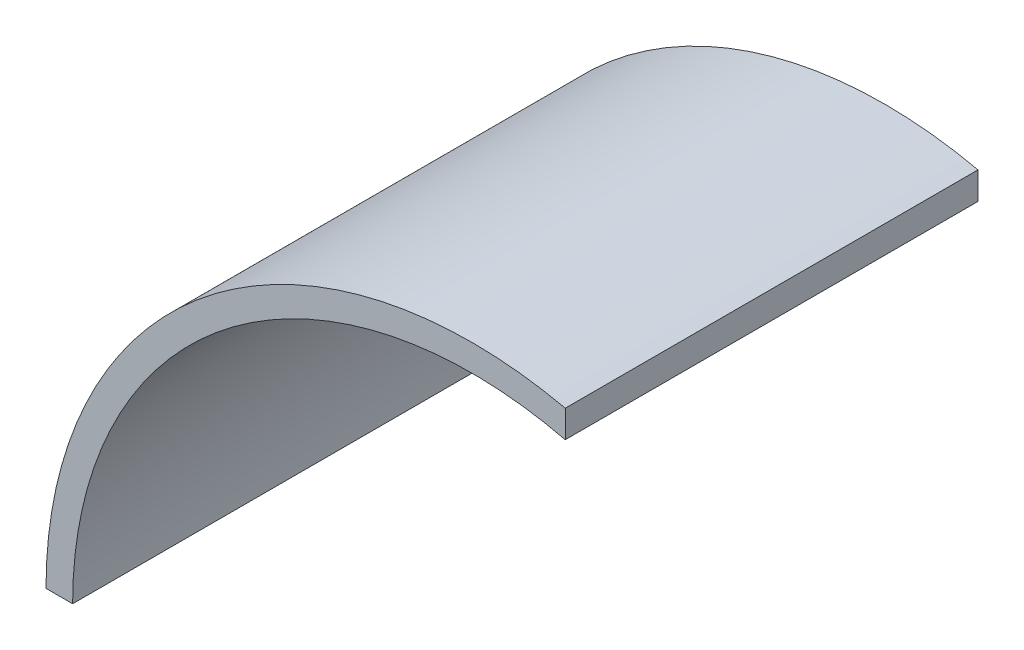
SolidWorks part; units mm, degrees
material "201 Annealed Stainless Steel (SS)"
ref_plane "Front Plane" through (0, 0, 0) normal (0, 0, 1) x (1, 0, 0)
ref_plane "Top Plane" through (0, 0, 0) normal (0, 1, 0) x (1, 0, 0)
ref_plane "Right Plane" through (0, 0, 0) normal (1, 0, 0) x (0, 0, -1)
sketch "Sketch1" plane through (0, 0, 0) normal (0, 0, 1) x (1, 0, 0)
  line L0 (0, 0) -> (0, -160) construction
  line L2 (0, 0) -> (101.5936, 0) construction
  line L3 (35, 113.7839) -> (35, -22.985) construction
  line L5 (35, 156.1249) -> (35, 145.8595)
  line L7 (0, 0) -> (-150, 0) construction
  line L10 (32.5, 146.4368) -> (32.5, 156.6645) construction
  line L25 (-160, 0) -> (-150, 0)
  circle A0 centre (0, 0) radius 150 construction
  circle A1 centre (0, 0) radius 160 construction
  arc A2 (-150, 0) -> (35, 145.8595) centre (0, 0) cw
  arc A3 (-160, 0) -> (35, 156.1249) centre (0, 0) cw
  dimension "D1" = 300
  dimension "D2" = 320
  dimension "D3" = 35
  dimension "D4" = 5
extrude "Inner Ring - Left Side" add sketch "Sketch1" along normal blind 155
